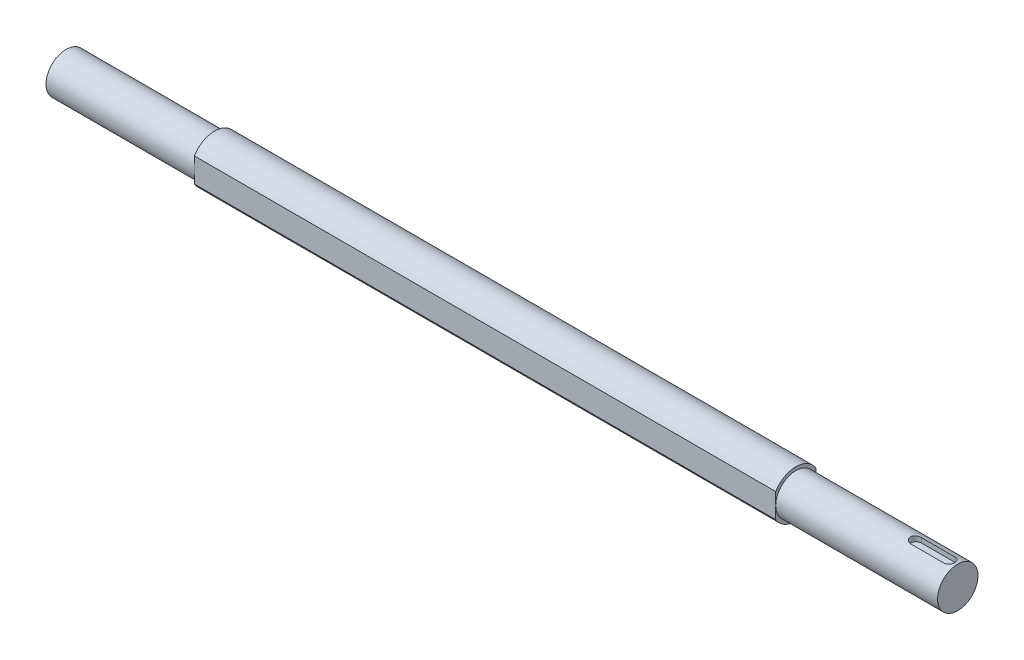
SolidWorks part; units mm, degrees
ref_plane "Front Plane" through (0, 0, 0) normal (0, 0, 1) x (1, 0, 0)
ref_plane "Top Plane" through (0, 0, 0) normal (0, 1, 0) x (1, 0, 0)
ref_plane "Right Plane" through (0, 0, 0) normal (1, 0, 0) x (0, 0, -1)
sketch "Çizim1" plane through (0, 0, 0) normal (0, 0, 1) x (1, 0, 0)
  line L0 (-330.5, 0) -> (330.5, 0)
  line L1 (-330.5, 0) -> (-330.5, 15)
  line L2 (-330.5, 15) -> (-220.5, 15)
  line L3 (-220.5, 15) -> (-220.5, 17.5)
  line L4 (-220.5, 17.5) -> (210.5, 17.5)
  line L5 (210.5, 17.5) -> (210.5, 15)
  line L6 (210.5, 15) -> (330.5, 15)
  line L7 (330.5, 15) -> (330.5, 0)
  point P4 (0, 0)
  dimension "D1" = 110
  dimension "D2" = 15
  dimension "D3" = 431
  dimension "D4" = 120
  dimension "D5" = 17.5
revolve "Döndür1" add sketch "Çizim1" angle 360 about L0
sketch "Çizim2" plane through (-220.5, 0, 0) normal (-1, 0, 0) x (0, 0, 1)
  line L0 (-15, 9.0139) -> (-15, -9.0139)
  line L1 (0, 0) -> (0, 4.7116) construction
  line L2 (15, 9.0139) -> (15, -9.0139)
  circle A2 centre (0, 0) radius 17.5 construction
  arc A3 (-15, 9.0139) -> (-15, -9.0139) centre (0, 0) ccw
  circle A4 centre (0, 0) radius 15 construction
  arc A5 (15, 9.0139) -> (15, -9.0139) centre (0, 0) cw
  point P3 (-15, 0)
extrude "Kes-Ekstrüzyon1" cut sketch "Çizim2" against normal up to surface (431 mm away) up to face at (210.5, -17.5, 0)
ref_plane "Düzlem1" through (0, 15, 0) normal (0, 1, 0) x (1, 0, 0)
sketch "Çizim3" plane through (0, 15, 0) normal (0, 1, 0) x (1, 0, 0)
  line L0 (324.5, 0) -> (299.5, 0) construction
  line L1 (324.5, -4) -> (299.5, -4)
  line L2 (324.5, 4) -> (299.5, 4)
  line L3 (330.5, -15) -> (330.5, 15) construction
  arc A0 (324.5, -4) -> (324.5, 4) centre (324.5, 0) ccw
  arc A1 (299.5, 4) -> (299.5, -4) centre (299.5, 0) ccw
  point P3 (312, 0)
  dimension "D1" = 8
  dimension "D2" = 6
  dimension "D3" = 25
extrude "Kes-Ekstrüzyon2" cut sketch "Çizim3" against normal blind 4
